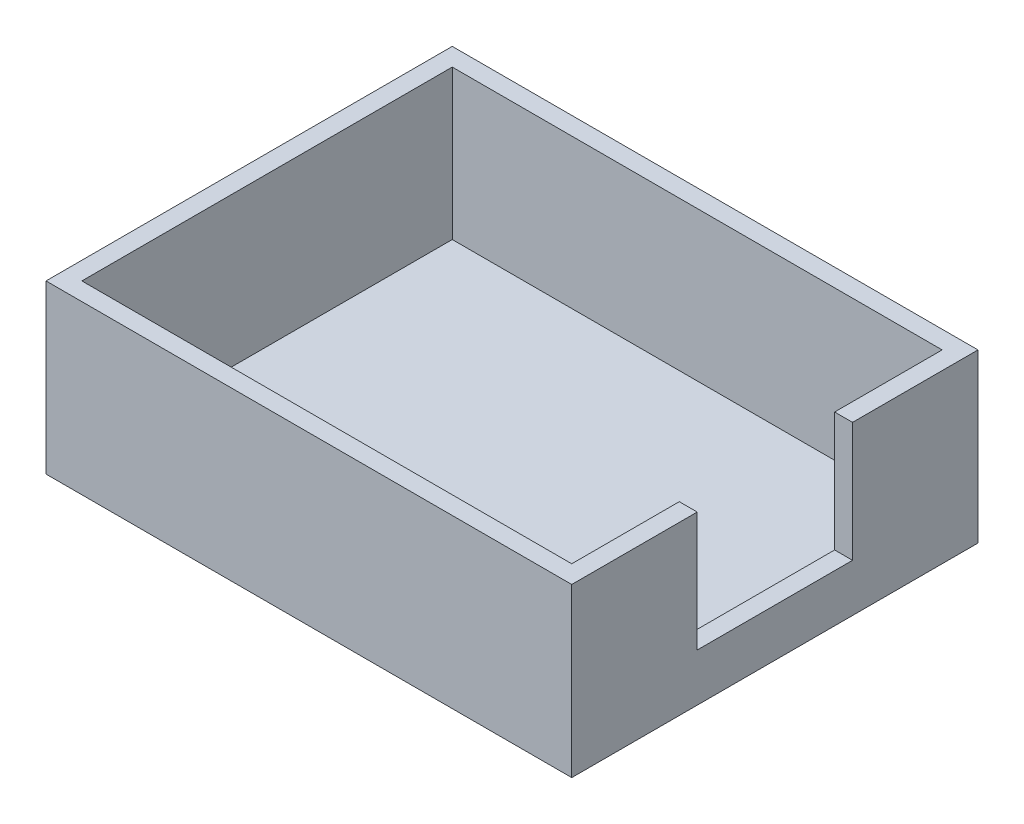
SolidWorks part; units mm, degrees
ref_plane "Plan de face" through (0, 0, 0) normal (0, 0, 1) x (1, 0, 0)
ref_plane "Plan de dessus" through (0, 0, 0) normal (0, 1, 0) x (1, 0, 0)
ref_plane "Plan de droite" through (0, 0, 0) normal (1, 0, 0) x (0, 0, -1)
sketch "Esquisse1" plane through (0, 0, 0) normal (0, 1, 0) x (1, 0, 0)
  line L1 (-22, 17) -> (22, 17)
  line L2 (-22, 17) -> (-22, -17)
  line L3 (-22, -17) -> (22, -17)
  line L4 (22, 17) -> (22, -17)
  line L5 (-22, 17) -> (22, -17) construction
  line L6 (-22, -17) -> (22, 17) construction
  point P0 (0, 0)
  dimension "D1" = 34
  dimension "D2" = 44
extrude "Boss.-Extru.1" add sketch "Esquisse1" along normal blind 14
shell "Coque1" thickness 1.5
sketch "Esquisse2" plane through (0, 14, 0) normal (0, 1, 0) x (1, 0, 0)
  line L6 (20.5, -15.5) -> (20.5, 15.5) construction
  line L7 (20.5, 6.5) -> (22, 6.5)
  line L8 (20.5, 6.5) -> (20.5, -6.5)
  line L9 (20.5, -6.5) -> (22, -6.5)
  line L10 (22, 6.5) -> (22, -6.5)
  line L11 (22, -17) -> (22, 17) construction
  point P8 (20.5, 0)
  dimension "D1" = 13
extrude "Enlèv. mat.-Extru.1" cut sketch "Esquisse2" against normal blind 10
